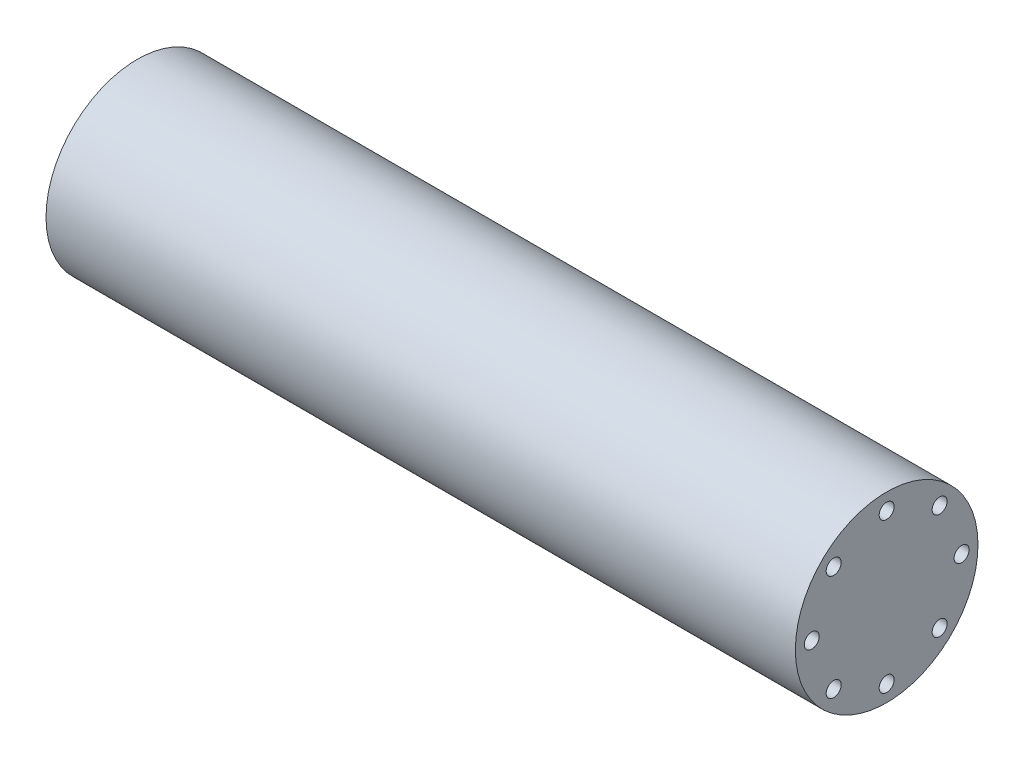
SolidWorks part; units mm, degrees
ref_plane "정면" through (0, 0, 0) normal (0, 0, 1) x (1, 0, 0)
ref_plane "윗면" through (0, 0, 0) normal (0, 1, 0) x (1, 0, 0)
ref_plane "우측면" through (0, 0, 0) normal (1, 0, 0) x (0, 0, -1)
ref_plane "평면1" through (0, 0, 0) normal (0, 0, -1) x (-1, 0, 0)
sketch "스케치1" plane through (0, 0, 0) normal (0, 0, -1) x (-1, 0, 0)
  line L0 (-80, 9.75) -> (-80, 0)
  line L1 (-80, 0) -> (0, 0)
  line L2 (0, 0) -> (0, 9.75)
  line L3 (0, 9.75) -> (-80, 9.75)
  line L4 (-80, 0) -> (0, 0) construction
revolve "회전1" add sketch "스케치1" angle 360 about L4
hole_wizard "Ø1.6 (1.6) 지름 구멍1" positions "스케치3" profile "스케치2" hole size "Ø1.6" standard "Ansi Metric"
sketch "스케치3" plane through (0, 0, 0) normal (-1, 0, 0) x (0, 0, 1)
  point P0 (0, 8)
  point P1 (-5.6569, 5.6569)
  point P2 (-8, 0)
  point P3 (-5.6569, -5.6569)
  point P4 (0, -8)
  point P5 (5.6569, -5.6569)
  point P6 (8, 0)
  point P7 (5.6569, 5.6569)
sketch "스케치2" plane through (0, 8, 0) normal (0, 1, 0) x (0, 0, 1)
  line L0 (0, 0) -> (0, 15.6807)
  line L1 (0, 15.6807) -> (0.8, 15.2)
  line L2 (0.8, 15.2) -> (0.8, 0)
  line L5 (0.8, 0) -> (0, 0)
  line L10 (0, 15.6807) -> (-0.8, 15.2) construction
  line L11 (0, -6.35) -> (0, 107.95) construction
  dimension "구멍 지름" = 1.6
  dimension "구멍 깊이" = 15.2
  dimension "드릴 각도" = 118
hole_wizard "Ø1.6 (1.6) 지름 구멍2" positions "스케치5" profile "스케치4" hole size "Ø1.6" standard "Ansi Metric"
sketch "스케치5" plane through (80, 0, 0) normal (1, 0, 0) x (0, 0, -1)
  point P0 (0, 8)
  point P1 (5.6569, 5.6569)
  point P2 (8, 0)
  point P3 (5.6569, -5.6569)
  point P4 (0, -8)
  point P5 (-5.6569, -5.6569)
  point P6 (-8, 0)
  point P7 (-5.6569, 5.6569)
sketch "스케치4" plane through (80, 8, 0) normal (0, 1, 0) x (0, 0, -1)
  line L0 (0, 0) -> (0, 15.6807)
  line L1 (0, 15.6807) -> (0.8, 15.2)
  line L2 (0.8, 15.2) -> (0.8, 0)
  line L5 (0.8, 0) -> (0, 0)
  line L10 (0, 15.6807) -> (-0.8, 15.2) construction
  line L11 (0, -6.35) -> (0, 107.95) construction
  dimension "구멍 지름" = 1.6
  dimension "구멍 깊이" = 15.2
  dimension "드릴 각도" = 118
